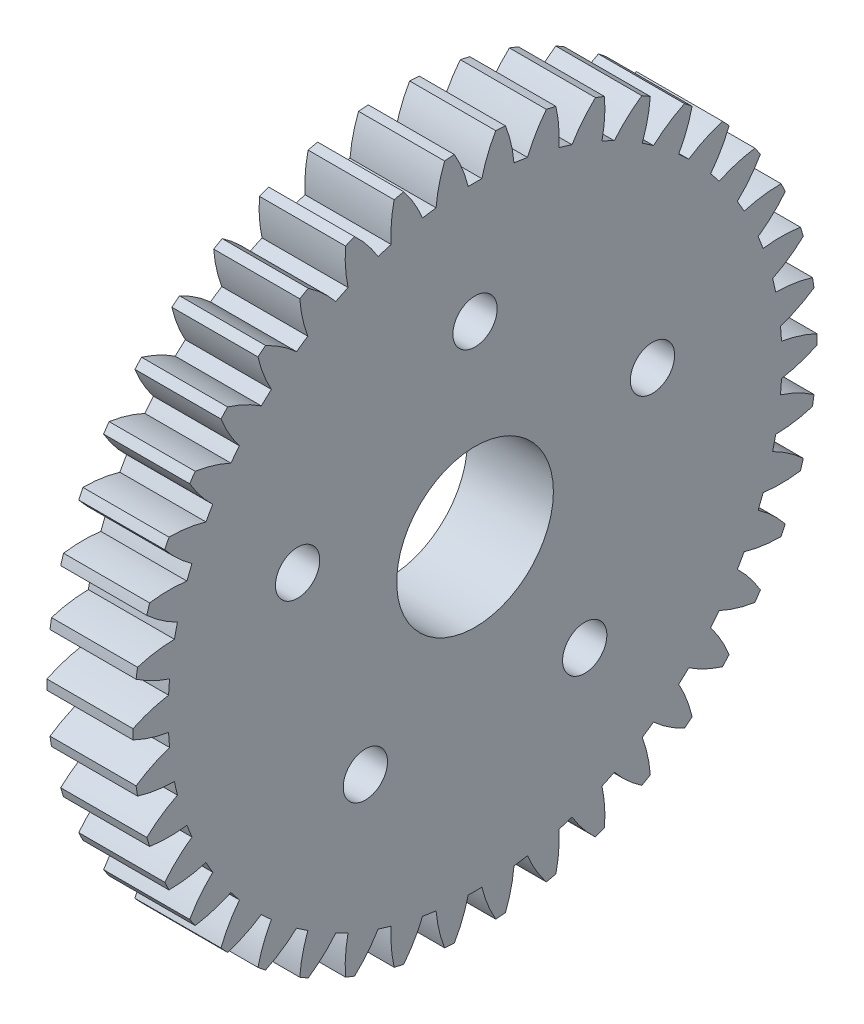
SolidWorks part; units mm, degrees
ref_plane "Plane1" through (0, 0, 0) normal (0, 0, 1) x (1, 0, 0)
ref_plane "Plane2" through (0, 0, 0) normal (0, 1, 0) x (1, 0, 0)
ref_plane "Plane3" through (0, 0, 0) normal (1, 0, 0) x (0, 0, -1)
sketch "HoldingSke" plane through (0, 0, 0) normal (0, 1, 0) x (1, 0, 0)
  line L0 (0, 0) -> (604.0281, -543.8694)
  line L1 (-15, 0) -> (100, 0) construction
  line L2 (0, 0) -> (-2.1039, 2.3779)
  line L3 (0, 0) -> (-11.863, 4.5341)
  line L4 (0, 0) -> (6.4178, 5.7786)
  line L5 (0, 0) -> (-47.5972, -17.7524)
  line L6 (0, 0) -> (-3.6426, -2.4577)
  line L7 (-2.1039, 2.3779) -> (8.8308, 51.9871)
  line L8 (-76.2, 54.61) -> (-75.184, 54.61)
  line L9 (-71.009, 38.7566) -> (-53.1078, 45.2721)
  line L10 (-76.2, 71.12) -> (104.1128, 71.12)
  line L11 (0, 0) -> (-4.3942, 0)
  line L12 (-76.2, 101.6) -> (-76.1716, 101.6)
  line L13 (24.9733, 27.94) -> (52.9518, 28.4284)
  line L14 (24.9733, 27.94) -> (25.0241, 27.9398)
  line L15 (24.9733, 27.94) -> (100.4021, 29.52)
  circle A0 centre (0, 0) radius 0.3969
  circle A1 centre (0, 0) radius 15.6655
  circle A2 centre (0, 0) radius 38.1
  circle A3 centre (0, 0) radius 0.3969
  dimension "MHD" = 31.3309
  dimension "Hub_dia" = 76.2
  dimension "Bore" = 0.7937
  dimension "MBD" = 0.7937
  dimension "Num_teeth" = 42
  dimension "Pitch_radius" = 180.3128
  dimension "Pitch" = 812.8
  dimension "Width" = 4.3942
  dimension "Overall_len" = 50.8
  dimension "Show_teeth" = 42
  dimension "Thickness" = 4.3942
  dimension "OAL" = 50.8001
  dimension "T_dim" = 1.016
  dimension "Ap" = 20
  dimension "H" = 19.05
  dimension "Backlash" = 0.0284
  dimension "Addendum_fac" = 1
  dimension "Dedendum_fac" = 1.2
  dimension "Clearance_fac" = 0.2
  dimension "Dedendum_add" = 0.0508
sketch "BasProSke" plane through (0, 0, 0) normal (0, 1, 0) x (1, 0, 0)
  line L0 (-10, 0) -> (60, 0) construction
  line L1 (0, 0) -> (0, 17.4625)
  line L2 (0, 0) -> (4.3942, 0)
  line L3 (4.3942, 0) -> (4.3942, 17.4625)
  line L4 (4.3942, 17.4625) -> (0, 17.4625)
  dimension "Diameter" = 34.925
  dimension "Thickness" = 4.3942
revolve "Base-Revolve" add sketch "BasProSke" angle 360 about L0
sketch "TooCutSke" plane through (0, 0, 0) normal (1, 0, 0) x (0, 0, -1)
  line L1 (0, 0) -> (0, 107) construction
  line L2 (0, 0) -> (-0.673, 16.6552) construction
  line L3 (0, 0) -> (-2.4898, 33.2246) construction
  line L4 (-0.673, 16.6552) -> (-1.2449, 16.6123) construction
  arc A0 (0.3488, 15.6616) -> (-0.3488, 15.6616) centre (0, 0) ccw
  arc A1 (1.0703, 17.4551) -> (-1.0703, 17.4551) centre (0, 0) ccw
  circle A2 centre (0, 0) radius 16.6687 construction
  circle A3 centre (0, 0) radius 15.6635 construction
  arc A4 (-0.3488, 15.6616) -> (-1.0703, 17.4551) centre (-6.8299, 14.096) ccw
  arc A5 (1.0703, 17.4551) -> (0.3488, 15.6616) centre (6.8299, 14.096) ccw
  dimension "Root_dia" = 31.3309
  dimension "Overcut_dia" = 34.9758
  dimension "Pitch_dia" = 33.3375
  dimension "Base_dia" = 31.327
  dimension "Flank_rad" = 6.6675
  dimension "Half_ang" = 4.286
  dimension "Half_CT" = 0.5735
extrude "ToothCut" cut sketch "TooCutSke" along normal through all
fillet "Breaks" [suppressed] radius 0.0159
fillet "RootFillets" [suppressed] radius 0.2095
pattern_circular "TeethCuts" count 42 every 8.571 about axis through (-10, 0, 0) along (1, 0, 0) of "ToothCut", "RootFillets", "Breaks"
sketch "HubNeaOneSke" plane through (0, 0, 0) normal (-1, 0, 0) x (0, 0, 1)
  circle A0 centre (0, 0) radius 15.6655
  dimension "Diameter" = 31.3309
extrude "HubNearOne" [suppressed] add sketch "HubNeaOneSke" along normal blind 46.4059
sketch "HubNeaBotSke" plane through (0, 0, 0) normal (-1, 0, 0) x (0, 0, 1)
  circle A0 centre (0, 0) radius 15.6655
  dimension "Diameter" = 31.3309
extrude "HubNearBoth" [suppressed] add sketch "HubNeaBotSke" along normal blind 23.2029
ref_plane "FarPln" through (4.3942, 0, 0) normal (1, 0, 0) x (0, 0, -1)
sketch "HubFarSke" plane through (4.3942, 0, 0) normal (1, 0, 0) x (0, 0, -1)
  circle A0 centre (0, 0) radius 15.6655
  dimension "Diameter" = 31.3309
extrude "HubFar" [suppressed] add sketch "HubFarSke" along normal blind 23.2029
sketch "BorSke" plane through (0, 0, 0) normal (1, 0, 0) x (0, 0, -1)
  circle A0 centre (0, 0) radius 0.3969
  dimension "Diameter" = 0.7937
extrude "Bore" cut sketch "BorSke" along normal mid plane 101.6001
sketch "KeySke" plane through (0, 0, 0) normal (1, 0, 0) x (0, 0, -1)
  line L0 (-0.127, 0) -> (-0.127, 0.6191)
  line L1 (-0.127, 0.6191) -> (0.127, 0.6191)
  line L2 (0.127, 0.6191) -> (0.127, 0)
  line L3 (0, 0) -> (0, 34) construction
  line L4 (-0.127, 0) -> (0.127, 0)
  dimension "Offset" = 0.6191
  dimension "Width" = 0.254
extrude "Keyway" [suppressed] cut sketch "KeySke" along normal mid plane 101.6001
pattern_circular "Keyway2" [suppressed] count 2 every 90 about axis through (-10, 0, 0) along (1, 0, 0)
sketch "Sketch1" plane through (4.3942, 0, 0) normal (1, 0, 0) x (0, 0, -1)
  circle A0 centre (0, 0) radius 4
  circle A1 centre (0, 9.525) radius 1.1303
  circle A2 centre (9.0588, 2.9434) radius 1.1303
  circle A3 centre (5.5987, -7.7059) radius 1.1303
  circle A4 centre (-5.5987, -7.7059) radius 1.1303
  circle A5 centre (-9.0588, 2.9434) radius 1.1303
  point P15 (0, 0)
  dimension "D1" = 8
  dimension "D2" = 2.2606
  dimension "D3" = 9.525
  dimension "D4" = 5
extrude "Cut-Extrude1" cut sketch "Sketch1" against normal blind 7.366
equation "' \"Pitch@HoldingSke\" = 4"
equation "' \"Num_teeth@HoldingSke\" = 12"
equation "' \"Ap@HoldingSke\" =  20"
equation "' \"Width@HoldingSke\" = 0.5"
equation "' \"Hub_dia@HoldingSke\"= 1"
equation "' \"Overall_len@HoldingSke\" = 1.0"
equation "' \"Bore@HoldingSke\" = 0.75"
equation "' \"T_dim@HoldingSke\" = 0.85"
equation "' \"Width@KeySke\" = 0.25"
equation "' \"Show_teeth@HoldingSke\" = 13"
equation "' \"Backlash@HoldingSke\" = 0.009"
equation "' \"Addendum_fac@HoldingSke\" = 1.0"
equation "' \"Dedendum_fac@HoldingSke\" = 1.25"
equation "' \"Dedendum_add@HoldingSke\" = 0.00005"
equation "' \"Clearance_fac@HoldingSke\" = 0.25"
equation "' \"Pitch@HoldingSke\" = 0.5"
equation "' \"Num_teeth@HoldingSke\" = 23"
equation "' \"Show_teeth@HoldingSke\" = 23"
equation "' \"Backlash@HoldingSke\" = 0.0375"
equation "\"Overcut_dia@TooCutSke\" = (\"Num_teeth@HoldingSke\" + 2 * \"Addendum_fac@HoldingSke\") / \"Pitch@HoldingSke\" + 0.002"
equation "\"Pitch_dia@TooCutSke\" = \"Num_teeth@HoldingSke\" / \"Pitch@HoldingSke\""
equation "\"Base_dia@TooCutSke\" = \"Num_teeth@HoldingSke\" / \"Pitch@HoldingSke\" * cos((\"Ap@HoldingSke\"  * 3.14159265 / 180))"
equation "\"Root_dia@TooCutSke\" = (\"Num_teeth@HoldingSke\" + 2) / \"Pitch@HoldingSke\" - 2 * (\"Addendum_fac@HoldingSke\" + \"Dedendum_fac@HoldingSke\") / \"Pitch@HoldingSke\" - \"Dedendum_add@HoldingSke\" * 2"
equation "\"Half_ang@TooCutSke\" = 180 / \"Num_teeth@HoldingSke\""
equation "\"Half_CT@TooCutSke\" = \"Num_teeth@HoldingSke\" / \"Pitch@HoldingSke\" * sin((3.14159265 / 2 / \"Num_teeth@HoldingSke\")) / 2 - 7 * \"Backlash@HoldingSke\" / 4"
equation "\"Flank_rad@TooCutSke\" = \"Num_teeth@HoldingSke\" / \"Pitch@HoldingSke\" / 5"
equation "\"Radius@RootFillets\" = \"Clearance_fac@HoldingSke\" / \"Pitch@HoldingSke\" + \"Dedendum_add@HoldingSke\""
equation "\"Break_rad@Breaks\" = 0.02 / \"Pitch@HoldingSke\""
equation "\"Thickness@HoldingSke\" = \"Width@HoldingSke\""
equation "\"OAL@HoldingSke\" = \"Thickness@HoldingSke\""
equation "\"MHD@HoldingSke\" = (\"Num_teeth@HoldingSke\" + 2) / \"Pitch@HoldingSke\" - 2 * (\"Addendum_fac@HoldingSke\" + \"Dedendum_fac@HoldingSke\")  / \"Pitch@HoldingSke\" - \"Dedendum_add@HoldingSke\" * 2"
equation "\"MBD@HoldingSke\" = (\"Num_teeth@HoldingSke\" + 2) / \"Pitch@HoldingSke\" - 2 * (\"Addendum_fac@HoldingSke\" + \"Dedendum_fac@HoldingSke\")  / \"Pitch@HoldingSke\" - \"Dedendum_add@HoldingSke\" * 2 - 0.002"
equation "\"MHD@HoldingSke\" = ((sgn( \"MHD@HoldingSke\" - \"Hub_dia@HoldingSke\" )-1)*( \"MHD@HoldingSke\" - \"Hub_dia@HoldingSke\" ))/-2+ \"Hub_dia@HoldingSke\""
equation "\"MBD@HoldingSke\" = ((sgn( \"MBD@HoldingSke\" - \"Bore@HoldingSke\" )-1)*( \"MBD@HoldingSke\" - \"Bore@HoldingSke\" ))/-2+ \"Bore@HoldingSke\""
equation "\"OAL@HoldingSke\" = ((sgn( \"OAL@HoldingSke\" - \"Overall_len@HoldingSke\" )+1)*( \"OAL@HoldingSke\" - \"Overall_len@HoldingSke\" ))/2 + \"Overall_len@HoldingSke\" + 0.000002"
equation "\"Num_teeth@TeethCuts\" = int( \"Show_teeth@HoldingSke\" ) + 1"
equation "\"Num_teeth@TeethCuts\" = ((sgn( \"Num_teeth@TeethCuts\" - \"Num_teeth@HoldingSke\" )-1)*( \"Num_teeth@TeethCuts\" - \"Num_teeth@HoldingSke\" ))/-2+ \"Num_teeth@HoldingSke\""
equation "\"Num_teeth@TeethCuts\" = ((sgn( \"Num_teeth@TeethCuts\" - 2.0)+1)*( \"Num_teeth@TeethCuts\" - 2.0))/2 +2.0"
equation "\"Angle@TeethCuts\" = 360.0 / \"Num_teeth@HoldingSke\""
equation "\"Diameter@BasProSke\" = (\"Num_teeth@HoldingSke\" + 2 * \"Addendum_fac@HoldingSke\") / \"Pitch@HoldingSke\""
equation "\"Thickness@BasProSke\"  = \"Thickness@HoldingSke\""
equation "' \"Fillet_rad@BasProSke\" =  \"Thickness@HoldingSke\" * 0.05"
equation "\"MHD@HoldingSke\" = ((sgn( \"MHD@HoldingSke\" - \"Root_dia@TooCutSke\" )-1)*( \"MHD@HoldingSke\" - \"Root_dia@TooCutSke\" ))/-2+ \"Root_dia@TooCutSke\""
equation "\"Diameter@HubNeaOneSke\" = \"MHD@HoldingSke\""
equation "\"Length@HubNearOne\" = \"OAL@HoldingSke\" - \"Thickness@BasProSke\""
equation "\"Diameter@HubNeaBotSke\" = \"MHD@HoldingSke\""
equation "\"Length@HubNearBoth\" = ( \"OAL@HoldingSke\" - \"Thickness@BasProSke\" ) / 2.0"
equation "\"Thickness@FarPln\" = \"Thickness@BasProSke\""
equation "\"Diameter@HubFarSke\" = \"MHD@HoldingSke\""
equation "\"Length@HubFar\" = ( \"OAL@HoldingSke\" - \"Thickness@BasProSke\" ) / 2.0"
equation "\"Diameter@BorSke\" = \"MBD@HoldingSke\""
equation "\"D1@Bore\" = \"OAL@HoldingSke\" * 2.0"
equation "\"D1@Keyway\" = \"OAL@HoldingSke\" * 2.0"
equation "\"Offset@KeySke\" = \"T_dim@HoldingSke\" - \"MBD@HoldingSke\" / 2.0"
